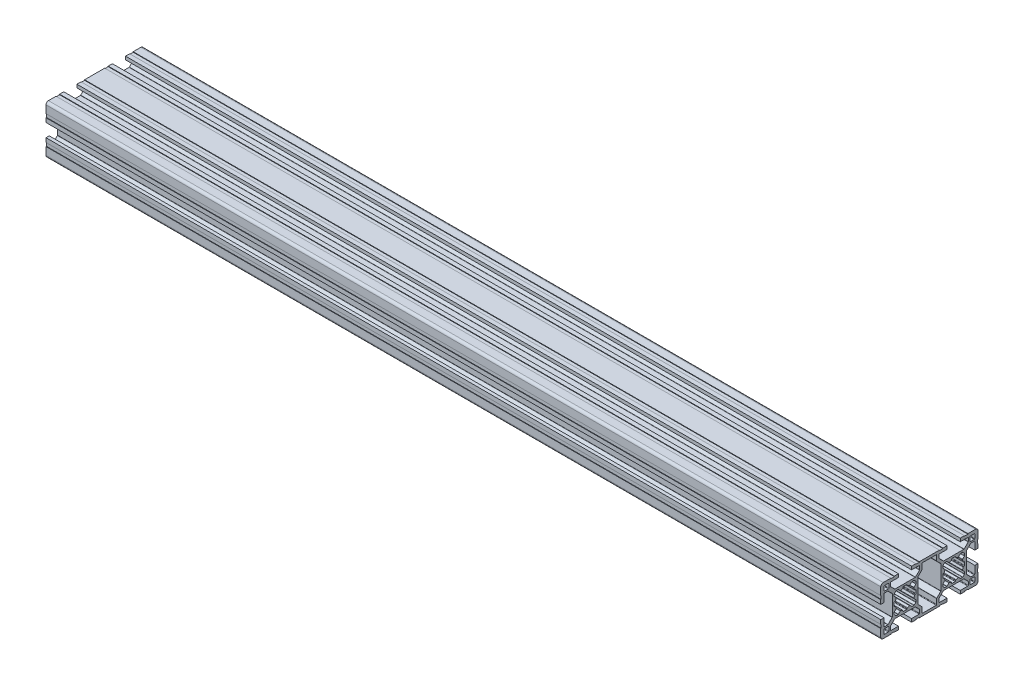
SolidWorks part; units mm, degrees
material "6063-T5 (Padrão)"
ref_plane "Plano frontal" through (0, 0, 0) normal (0, 0, 1) x (1, 0, 0)
ref_plane "Plano superior" through (0, 0, 0) normal (0, 1, 0) x (1, 0, 0)
ref_plane "Plano direito" through (0, 0, 0) normal (1, 0, 0) x (0, 0, -1)
sketch "Esboço1" plane through (0, 0, 0) normal (0, 0, 1) x (1, 0, 0)
  line L0 (-257.5, 0) -> (257.5, 0)
  point P4 (0, 0)
  dimension "D1" = 515
other "Retangular PF30-02 - PERFIL 3060 BÁSICO(1)"
ref_plane "Plano1" through (-257.5, 0, 0) normal (1, 0, 0) x (0, 1, 0)
sketch "Sketch11" plane through (-257.5, 0, 0) normal (1, 0, 0) x (0, 1, 0)
  line L0 (-9.8464, -4.5906) -> (-7.4222, -7.0149)
  line L1 (-7.21, -7.1028) -> (7.21, -7.1028)
  line L2 (7.4222, -7.0149) -> (9.8464, -4.5906)
  line L3 (10.0586, -4.5028) -> (13.2, -4.5028)
  line L4 (13.5, -4.2028) -> (13.5, 4.1972)
  line L5 (13.2, 4.4972) -> (10.0586, 4.4972)
  line L6 (9.8464, 4.5851) -> (7.4222, 7.0094)
  line L7 (7.21, 7.0972) -> (-7.21, 7.0972)
  line L8 (-7.4222, 7.0094) -> (-9.8464, 4.5851)
  line L9 (-10.0586, 4.4972) -> (-13.2, 4.4972)
  line L10 (-13.5, 4.1972) -> (-13.5, -4.2028)
  line L11 (-13.2, -4.5028) -> (-10.0586, -4.5028)
  line L12 (-6.7, 15.9528) -> (-6.7, 14.0528)
  line L13 (-6.1579, 16.2528) -> (-6.4, 16.2528)
  line L14 (-6.6121, 19.14) -> (-5.4871, 18.015)
  line L15 (-6.7, 20.4423) -> (-6.7, 19.3522)
  line L16 (-6.1319, 21.1347) -> (-6.6121, 20.6545)
  line L17 (-10.4678, 23.9149) -> (-7.9879, 21.435)
  line L18 (-12.7, 24.0028) -> (-10.6799, 24.0028)
  line L19 (-13, 19.0528) -> (-13, 23.7028)
  line L20 (-13, 19.0528) -> (-15, 19.0528)
  line L21 (6.7, 15.9528) -> (6.7, 14.0528)
  line L22 (7.9, 21.2229) -> (7.9, 8.7827)
  line L23 (15, 21.6028) -> (15, 19.0528)
  line L24 (-5.4396, 21.7028) -> (-4.3494, 21.7028)
  line L25 (-13, 25.3028) -> (-13, 27.7028)
  line L26 (-4.05, 28.0028) -> (-8.7, 28.0028)
  line L27 (-12.7, 28.0028) -> (-10.3, 28.0028)
  line L28 (-9, 27.7028) -> (-9, 25.6827)
  line L29 (-10, 27.7028) -> (-10, 25.3028)
  line L30 (-8.9121, 25.4705) -> (-6.4322, 22.9906)
  line L31 (15, 23.8028) -> (14.7, 23.8028)
  line L32 (14.7, 23.8028) -> (14.7, 21.6028)
  line L33 (15, 28.5028) -> (15, 23.8028)
  line L34 (8.8, 30.0028) -> (13.5, 30.0028)
  line L35 (8.8, 29.7028) -> (6.6, 29.7028)
  line L36 (4.05, 30.0028) -> (6.6, 30.0028)
  line L37 (4.05, 28.0028) -> (4.05, 30.0028)
  line L38 (10.3, 25.0028) -> (12.7, 25.0028)
  line L39 (15, 21.6028) -> (14.7, 21.6028)
  line L40 (6.6, 30.0028) -> (6.6, 29.7028)
  line L41 (-6.1319, 21.1347) -> (-5.6517, 21.6149)
  line L42 (-4.1373, 21.6149) -> (-3.0123, 20.4899)
  line L43 (-1.25, 21.1607) -> (-1.25, 21.4028)
  line L44 (8.8, 30.0028) -> (8.8, 29.7028)
  line L45 (1.25, 21.1607) -> (1.25, 21.4028)
  line L46 (4.1373, 21.6149) -> (3.0123, 20.4899)
  line L47 (6.1319, 21.1347) -> (5.6517, 21.6149)
  line L48 (8.9121, 25.4705) -> (6.4322, 22.9906)
  line L49 (10, 27.7028) -> (10, 25.3028)
  line L50 (9, 27.7028) -> (9, 25.6827)
  line L51 (12.7, 28.0028) -> (10.3, 28.0028)
  line L52 (4.05, 28.0028) -> (8.7, 28.0028)
  line L53 (13, 25.3028) -> (13, 27.7028)
  line L54 (5.4396, 21.7028) -> (4.3494, 21.7028)
  line L55 (13, 19.0528) -> (15, 19.0528)
  line L56 (13, 19.0528) -> (13, 23.7028)
  line L57 (12.7, 24.0028) -> (10.6799, 24.0028)
  line L58 (10.4678, 23.9149) -> (7.9879, 21.435)
  line L59 (6.1319, 21.1347) -> (6.6121, 20.6545)
  line L60 (6.7, 20.4423) -> (6.7, 19.3522)
  line L61 (6.6121, 19.14) -> (5.4871, 18.015)
  line L62 (6.1579, 16.2528) -> (6.4, 16.2528)
  line L63 (-7.9, 8.7827) -> (-7.9, 21.2229)
  line L64 (-0.95, 8.3028) -> (0.95, 8.3028)
  line L65 (-15, 8.4028) -> (-15, 10.9528)
  line L66 (-15, 6.2028) -> (-14.7, 6.2028)
  line L67 (-14.7, 6.2028) -> (-14.7, 8.4028)
  line L68 (-15, -14.9972) -> (15, -14.9972) construction
  line L69 (-6.1579, -13.7472) -> (-6.4, -13.7472)
  line L70 (-6.6121, -10.86) -> (-5.4871, -11.985)
  line L71 (-6.7, -9.5577) -> (-6.7, -10.6478)
  line L72 (-15, 8.4028) -> (-14.7, 8.4028)
  line L73 (-0.95, -21.6972) -> (0.95, -21.6972)
  line L74 (-6.1319, -8.8653) -> (-6.6121, -9.3455)
  line L75 (6.1579, 13.7528) -> (6.4, 13.7528)
  line L76 (6.6121, 10.8655) -> (5.4871, 11.9905)
  line L77 (6.7, 9.5632) -> (6.7, 10.6534)
  line L78 (6.1319, 8.8709) -> (6.6121, 9.3511)
  line L79 (10.4678, 6.0906) -> (7.9879, 8.5705)
  line L80 (12.7, 6.0028) -> (10.6799, 6.0028)
  line L81 (13, 10.9528) -> (13, 6.3028)
  line L82 (13, 10.9528) -> (15, 10.9528)
  line L83 (5.4396, 8.3028) -> (4.3494, 8.3028)
  line L84 (-10.4678, -6.0851) -> (-7.9879, -8.565)
  line L85 (-8.8, 30.0028) -> (-8.8, 29.7028)
  line L86 (-12.7, -5.9972) -> (-10.6799, -5.9972)
  line L87 (-13, -10.9472) -> (-13, -6.2972)
  line L88 (-13, -10.9472) -> (-15, -10.9472)
  line L89 (15, -8.3972) -> (15, -10.9472)
  line L90 (-5.4396, -8.2972) -> (-4.3494, -8.2972)
  line L91 (6.1319, 8.8709) -> (5.6517, 8.3906)
  line L92 (4.1373, 8.3906) -> (3.0123, 9.5156)
  line L93 (1.25, 8.8448) -> (1.25, 8.6028)
  line L94 (-15, -21.5972) -> (-15, -19.0472)
  line L95 (-6.6, 30.0028) -> (-6.6, 29.7028)
  line L96 (-1.25, 8.8448) -> (-1.25, 8.6028)
  line L97 (-4.1373, 8.3906) -> (-3.0123, 9.5156)
  line L98 (-6.1319, 8.8709) -> (-5.6517, 8.3906)
  line L99 (-15, -23.7972) -> (-14.7, -23.7972)
  line L100 (15, 8.4028) -> (14.7, 8.4028)
  line L101 (-14.7, -23.7972) -> (-14.7, -21.5972)
  line L102 (-15, -28.4972) -> (-15, -23.7972)
  line L103 (-8.8, -29.9972) -> (-13.5, -29.9972)
  line L104 (-8.8, -29.6972) -> (-6.6, -29.6972)
  line L105 (-4.05, -29.9972) -> (-6.6, -29.9972)
  line L106 (14.7, 6.2028) -> (14.7, 8.4028)
  line L107 (15, 6.2028) -> (14.7, 6.2028)
  line L108 (-4.05, -27.9972) -> (-4.05, -29.9972)
  line L109 (-10.3, -24.9972) -> (-12.7, -24.9972)
  line L110 (-6.2201, -22.8972) -> (6.2201, -22.8972)
  line L111 (-15, -21.5972) -> (-14.7, -21.5972)
  line L112 (15, -6.1972) -> (14.7, -6.1972)
  line L113 (-15, 21.6028) -> (-14.7, 21.6028)
  line L114 (-6.2201, 22.9028) -> (6.2201, 22.9028)
  line L115 (-10.3, 25.0028) -> (-12.7, 25.0028)
  line L116 (-4.05, 28.0028) -> (-4.05, 30.0028)
  line L117 (-4.05, 30.0028) -> (-6.6, 30.0028)
  line L118 (-8.8, 29.7028) -> (-6.6, 29.7028)
  line L119 (0, 29.9972) -> (0, -29.9972) construction
  line L120 (-15, 15.0028) -> (15, 15.0028) construction
  line L121 (-8.8, 30.0028) -> (-13.5, 30.0028)
  line L122 (-15, 28.5028) -> (-15, 23.8028)
  line L123 (-14.7, 23.8028) -> (-14.7, 21.6028)
  line L124 (-15, 23.8028) -> (-14.7, 23.8028)
  line L125 (-15, 21.6028) -> (-15, 19.0528)
  line L126 (14.7, -6.1972) -> (14.7, -8.3972)
  line L127 (-5.4396, 8.3028) -> (-4.3494, 8.3028)
  line L128 (15, 8.4028) -> (15, 10.9528)
  line L129 (15, 6.2028) -> (15, -6.1972)
  line L130 (-13, 10.9528) -> (-15, 10.9528)
  line L131 (-13, 10.9528) -> (-13, 6.3028)
  line L132 (-12.7, 6.0028) -> (-10.6799, 6.0028)
  line L133 (-10.4678, 6.0906) -> (-7.9879, 8.5705)
  line L134 (-6.1319, 8.8709) -> (-6.6121, 9.3511)
  line L135 (-0.95, 21.7028) -> (0.95, 21.7028)
  line L136 (-6.7, 9.5632) -> (-6.7, 10.6534)
  line L137 (-6.6121, 10.8655) -> (-5.4871, 11.9905)
  line L138 (-6.1579, 13.7528) -> (-6.4, 13.7528)
  line L139 (15, 0.0028) -> (-15, 0.0028) construction
  line L140 (15, -8.3972) -> (14.7, -8.3972)
  line L141 (-6.1319, -8.8653) -> (-5.6517, -8.3851)
  line L142 (-4.1373, -8.3851) -> (-3.0123, -9.5101)
  line L143 (-1.25, -8.8393) -> (-1.25, -8.5972)
  line L144 (-6.6, -29.9972) -> (-6.6, -29.6972)
  line L145 (1.25, -8.8393) -> (1.25, -8.5972)
  line L146 (4.1373, -8.3851) -> (3.0123, -9.5101)
  line L147 (6.1319, -8.8653) -> (5.6517, -8.3851)
  line L148 (-8.8, -29.9972) -> (-8.8, -29.6972)
  line L149 (5.4396, -8.2972) -> (4.3494, -8.2972)
  line L150 (13, -10.9472) -> (15, -10.9472)
  line L151 (13, -10.9472) -> (13, -6.2972)
  line L152 (12.7, -5.9972) -> (10.6799, -5.9972)
  line L153 (10.4678, -6.0851) -> (7.9879, -8.565)
  line L154 (6.1319, -8.8653) -> (6.6121, -9.3455)
  line L155 (6.7, -9.5577) -> (6.7, -10.6478)
  line L156 (6.6121, -10.86) -> (5.4871, -11.985)
  line L157 (6.1579, -13.7472) -> (6.4, -13.7472)
  line L158 (-15, -8.3972) -> (-14.7, -8.3972)
  line L159 (-15, 6.2028) -> (-15, -6.1972)
  line L160 (-14.7, -6.1972) -> (-14.7, -8.3972)
  line L161 (-15, -6.1972) -> (-14.7, -6.1972)
  line L162 (-15, -8.3972) -> (-15, -10.9472)
  line L163 (-0.95, -8.2972) -> (0.95, -8.2972)
  line L164 (-7.9, -8.7771) -> (-7.9, -21.2173)
  line L165 (6.1579, -16.2472) -> (6.4, -16.2472)
  line L166 (6.6121, -19.1345) -> (5.4871, -18.0095)
  line L167 (6.7, -20.4368) -> (6.7, -19.3466)
  line L168 (6.1319, -21.1291) -> (6.6121, -20.6489)
  line L169 (10.4678, -23.9094) -> (7.9879, -21.4295)
  line L170 (12.7, -23.9972) -> (10.6799, -23.9972)
  line L171 (13, -19.0472) -> (13, -23.6972)
  line L172 (13, -19.0472) -> (15, -19.0472)
  line L173 (5.4396, -21.6972) -> (4.3494, -21.6972)
  line L174 (13, -25.2972) -> (13, -27.6972)
  line L175 (4.05, -27.9972) -> (8.7, -27.9972)
  line L176 (12.7, -27.9972) -> (10.3, -27.9972)
  line L177 (9, -27.6972) -> (9, -25.6771)
  line L178 (10, -27.6972) -> (10, -25.2972)
  line L179 (8.9121, -25.465) -> (6.4322, -22.9851)
  line L180 (6.1319, -21.1291) -> (5.6517, -21.6093)
  line L181 (4.1373, -21.6093) -> (3.0123, -20.4844)
  line L182 (1.25, -21.1551) -> (1.25, -21.3972)
  line L183 (8.8, -29.9972) -> (8.8, -29.6972)
  line L184 (-1.25, -21.1551) -> (-1.25, -21.3972)
  line L185 (-4.1373, -21.6093) -> (-3.0123, -20.4844)
  line L186 (-6.1319, -21.1291) -> (-5.6517, -21.6093)
  line L187 (6.6, -29.9972) -> (6.6, -29.6972)
  line L188 (15, -21.5972) -> (14.7, -21.5972)
  line L189 (10.3, -24.9972) -> (12.7, -24.9972)
  line L190 (4.05, -27.9972) -> (4.05, -29.9972)
  line L191 (4.05, -29.9972) -> (6.6, -29.9972)
  line L192 (8.8, -29.6972) -> (6.6, -29.6972)
  line L193 (8.8, -29.9972) -> (13.5, -29.9972)
  line L194 (15, -28.4972) -> (15, -23.7972)
  line L195 (14.7, -23.7972) -> (14.7, -21.5972)
  line L196 (15, -23.7972) -> (14.7, -23.7972)
  line L197 (-8.9121, -25.465) -> (-6.4322, -22.9851)
  line L198 (-10, -27.6972) -> (-10, -25.2972)
  line L199 (-9, -27.6972) -> (-9, -25.6771)
  line L200 (-12.7, -27.9972) -> (-10.3, -27.9972)
  line L201 (-4.05, -27.9972) -> (-8.7, -27.9972)
  line L202 (-13, -25.2972) -> (-13, -27.6972)
  line L203 (-5.4396, -21.6972) -> (-4.3494, -21.6972)
  line L204 (15, -21.5972) -> (15, -19.0472)
  line L205 (7.9, -21.2173) -> (7.9, -8.7771)
  line L206 (6.7, -15.9472) -> (6.7, -14.0472)
  line L207 (-13, -19.0472) -> (-15, -19.0472)
  line L208 (-13, -19.0472) -> (-13, -23.6972)
  line L209 (-12.7, -23.9972) -> (-10.6799, -23.9972)
  line L210 (-10.4678, -23.9094) -> (-7.9879, -21.4295)
  line L211 (-6.1319, -21.1291) -> (-6.6121, -20.6489)
  line L212 (-6.7, -20.4368) -> (-6.7, -19.3466)
  line L213 (-6.6121, -19.1345) -> (-5.4871, -18.0095)
  line L214 (-6.1579, -16.2472) -> (-6.4, -16.2472)
  line L215 (-6.7, -15.9472) -> (-6.7, -14.0472)
  arc A0 (-9.8464, -4.5906) -> (-10.0586, -4.5028) centre (-10.0586, -4.8028) ccw
  arc A1 (-7.4222, -7.0149) -> (-7.21, -7.1028) centre (-7.21, -6.8028) ccw
  arc A2 (7.21, -7.1028) -> (7.4222, -7.0149) centre (7.21, -6.8028) ccw
  arc A3 (10.0586, -4.5028) -> (9.8464, -4.5906) centre (10.0586, -4.8028) ccw
  arc A4 (13.2, -4.5028) -> (13.5, -4.2028) centre (13.2, -4.2028) ccw
  arc A5 (13.5, 4.1972) -> (13.2, 4.4972) centre (13.2, 4.1972) ccw
  arc A6 (9.8464, 4.5851) -> (10.0586, 4.4972) centre (10.0586, 4.7972) ccw
  arc A7 (7.4222, 7.0094) -> (7.21, 7.0972) centre (7.21, 6.7972) ccw
  arc A8 (-7.21, 7.0972) -> (-7.4222, 7.0094) centre (-7.21, 6.7972) ccw
  arc A9 (-10.0586, 4.4972) -> (-9.8464, 4.5851) centre (-10.0586, 4.7972) ccw
  arc A10 (-13.2, 4.4972) -> (-13.5, 4.1972) centre (-13.2, 4.1972) ccw
  arc A11 (-13.5, -4.2028) -> (-13.2, -4.5028) centre (-13.2, -4.2028) ccw
  arc A12 (-6.4, 16.2528) -> (-6.7, 15.9528) centre (-6.4, 15.9528) ccw
  arc A13 (-5.867, 16.4795) -> (-6.1579, 16.2528) centre (-6.1579, 16.5528) cw
  arc A14 (-5.867, 16.4795) -> (-5.43, 17.6706) centre (0, 15.0028) cw
  arc A15 (-5.4871, 18.015) -> (-5.43, 17.6706) centre (-5.6993, 17.8029) cw
  arc A16 (-6.6121, 19.14) -> (-6.7, 19.3522) centre (-6.4, 19.3522) cw
  arc A17 (-6.6121, 20.6545) -> (-6.7, 20.4423) centre (-6.4, 20.4423) ccw
  arc A18 (-7.9879, 21.435) -> (-7.9, 21.2229) centre (-8.2, 21.2229) cw
  arc A19 (-10.6799, 24.0028) -> (-10.4678, 23.9149) centre (-10.6799, 23.7028) cw
  arc A20 (-13, 23.7028) -> (-12.7, 24.0028) centre (-12.7, 23.7028) cw
  arc A21 (13.5, 30.0028) -> (15, 28.5028) centre (13.5, 28.5028) cw
  arc A22 (1.25, 21.4028) -> (0.95, 21.7028) centre (0.95, 21.4028) ccw
  arc A23 (4.1373, 21.6149) -> (4.3494, 21.7028) centre (4.3494, 21.4028) cw
  arc A24 (1.4768, 20.8698) -> (1.25, 21.1607) centre (1.55, 21.1607) cw
  arc A25 (1.4768, 20.8698) -> (2.6678, 20.4328) centre (0, 15.0028) cw
  arc A26 (-10.3, 25.0028) -> (-10, 25.3028) centre (-10.3, 25.3028) ccw
  arc A27 (-6.4322, 22.9906) -> (-6.2201, 22.9028) centre (-6.2201, 23.2028) ccw
  arc A28 (-13, 25.3028) -> (-12.7, 25.0028) centre (-12.7, 25.3028) ccw
  arc A29 (-9, 25.6827) -> (-8.9121, 25.4705) centre (-8.7, 25.6827) ccw
  arc A30 (-10, 27.7028) -> (-10.3, 28.0028) centre (-10.3, 27.7028) ccw
  arc A31 (-8.7, 28.0028) -> (-9, 27.7028) centre (-8.7, 27.7028) ccw
  arc A32 (-12.7, 28.0028) -> (-13, 27.7028) centre (-12.7, 27.7028) ccw
  arc A33 (3.0123, 20.4899) -> (2.6678, 20.4328) centre (2.8001, 20.702) cw
  arc A34 (5.6517, 21.6149) -> (5.4396, 21.7028) centre (5.4396, 21.4028) ccw
  arc A35 (12.7, 28.0028) -> (13, 27.7028) centre (12.7, 27.7028) cw
  arc A36 (8.7, 28.0028) -> (9, 27.7028) centre (8.7, 27.7028) cw
  arc A37 (10, 27.7028) -> (10.3, 28.0028) centre (10.3, 27.7028) cw
  arc A38 (9, 25.6827) -> (8.9121, 25.4705) centre (8.7, 25.6827) cw
  arc A39 (13, 25.3028) -> (12.7, 25.0028) centre (12.7, 25.3028) cw
  arc A40 (6.4322, 22.9906) -> (6.2201, 22.9028) centre (6.2201, 23.2028) cw
  arc A41 (10.3, 25.0028) -> (10, 25.3028) centre (10.3, 25.3028) cw
  arc A42 (13, 23.7028) -> (12.7, 24.0028) centre (12.7, 23.7028) ccw
  arc A43 (10.6799, 24.0028) -> (10.4678, 23.9149) centre (10.6799, 23.7028) ccw
  arc A44 (7.9879, 21.435) -> (7.9, 21.2229) centre (8.2, 21.2229) ccw
  arc A45 (6.6121, 20.6545) -> (6.7, 20.4423) centre (6.4, 20.4423) cw
  arc A46 (6.6121, 19.14) -> (6.7, 19.3522) centre (6.4, 19.3522) ccw
  arc A47 (5.4871, 18.015) -> (5.43, 17.6706) centre (5.6993, 17.8029) ccw
  arc A48 (5.867, 16.4795) -> (5.43, 17.6706) centre (0, 15.0028) ccw
  arc A49 (5.867, 16.4795) -> (6.1579, 16.2528) centre (6.1579, 16.5528) ccw
  arc A50 (6.4, 16.2528) -> (6.7, 15.9528) centre (6.4, 15.9528) cw
  arc A51 (6.4, 13.7528) -> (6.7, 14.0528) centre (6.4, 14.0528) ccw
  arc A52 (-5.6517, 21.6149) -> (-5.4396, 21.7028) centre (-5.4396, 21.4028) cw
  arc A53 (-3.0123, 20.4899) -> (-2.6678, 20.4328) centre (-2.8001, 20.702) ccw
  arc A54 (-1.4768, 20.8698) -> (-2.6678, 20.4328) centre (0, 15.0028) ccw
  arc A55 (-1.4768, 20.8698) -> (-1.25, 21.1607) centre (-1.55, 21.1607) ccw
  arc A56 (-4.1373, 21.6149) -> (-4.3494, 21.7028) centre (-4.3494, 21.4028) ccw
  arc A57 (-6.4, 13.7528) -> (-6.7, 14.0528) centre (-6.4, 14.0528) cw
  arc A58 (-13.5, -29.9972) -> (-15, -28.4972) centre (-13.5, -28.4972) cw
  arc A59 (-1.25, 8.6028) -> (-0.95, 8.3028) centre (-0.95, 8.6028) ccw
  arc A60 (-4.1373, 8.3906) -> (-4.3494, 8.3028) centre (-4.3494, 8.6028) cw
  arc A61 (-1.4768, 9.1358) -> (-1.25, 8.8448) centre (-1.55, 8.8448) cw
  arc A62 (-1.4768, 9.1358) -> (-2.6678, 9.5728) centre (0, 15.0028) cw
  arc A63 (-3.0123, 9.5156) -> (-2.6678, 9.5728) centre (-2.8001, 9.3035) cw
  arc A64 (-5.6517, 8.3906) -> (-5.4396, 8.3028) centre (-5.4396, 8.6028) ccw
  arc A65 (5.867, 13.526) -> (6.1579, 13.7528) centre (6.1579, 13.4528) cw
  arc A66 (5.867, 13.526) -> (5.43, 12.3349) centre (0, 15.0028) cw
  arc A67 (5.4871, 11.9905) -> (5.43, 12.3349) centre (5.6993, 12.2026) cw
  arc A68 (6.6121, 10.8655) -> (6.7, 10.6534) centre (6.4, 10.6534) cw
  arc A69 (6.6121, 9.3511) -> (6.7, 9.5632) centre (6.4, 9.5632) ccw
  arc A70 (7.9879, 8.5705) -> (7.9, 8.7827) centre (8.2, 8.7827) cw
  arc A71 (10.6799, 6.0028) -> (10.4678, 6.0906) centre (10.6799, 6.3028) cw
  arc A72 (13, 6.3028) -> (12.7, 6.0028) centre (12.7, 6.3028) cw
  arc A73 (-5.867, -13.5205) -> (-6.1579, -13.7472) centre (-6.1579, -13.4472) cw
  arc A74 (-5.867, -13.5205) -> (-5.43, -12.3294) centre (0, -14.9972) cw
  arc A75 (-1.25, -21.3972) -> (-0.95, -21.6972) centre (-0.95, -21.3972) ccw
  arc A76 (-5.4871, -11.985) -> (-5.43, -12.3294) centre (-5.6993, -12.1971) cw
  arc A77 (-6.6121, -10.86) -> (-6.7, -10.6478) centre (-6.4, -10.6478) cw
  arc A78 (-6.6121, -9.3455) -> (-6.7, -9.5577) centre (-6.4, -9.5577) ccw
  arc A79 (-7.9879, -8.565) -> (-7.9, -8.7771) centre (-8.2, -8.7771) cw
  arc A80 (5.6517, 8.3906) -> (5.4396, 8.3028) centre (5.4396, 8.6028) cw
  arc A81 (3.0123, 9.5156) -> (2.6678, 9.5728) centre (2.8001, 9.3035) ccw
  arc A82 (-10.6799, -5.9972) -> (-10.4678, -6.0851) centre (-10.6799, -6.2972) cw
  arc A83 (-13, -6.2972) -> (-12.7, -5.9972) centre (-12.7, -6.2972) cw
  arc A84 (1.25, -8.5972) -> (0.95, -8.2972) centre (0.95, -8.5972) ccw
  arc A85 (4.1373, -8.3851) -> (4.3494, -8.2972) centre (4.3494, -8.5972) cw
  arc A86 (1.4768, -9.1302) -> (1.25, -8.8393) centre (1.55, -8.8393) cw
  arc A87 (1.4768, -9.1302) -> (2.6678, -9.5672) centre (0, -14.9972) cw
  arc A88 (3.0123, -9.5101) -> (2.6678, -9.5672) centre (2.8001, -9.2979) cw
  arc A89 (1.4768, 9.1358) -> (2.6678, 9.5728) centre (0, 15.0028) ccw
  arc A90 (1.4768, 9.1358) -> (1.25, 8.8448) centre (1.55, 8.8448) ccw
  arc A91 (4.1373, 8.3906) -> (4.3494, 8.3028) centre (4.3494, 8.6028) ccw
  arc A92 (1.25, 8.6028) -> (0.95, 8.3028) centre (0.95, 8.6028) cw
  arc A93 (5.6517, -8.3851) -> (5.4396, -8.2972) centre (5.4396, -8.5972) ccw
  arc A94 (-13, 6.3028) -> (-12.7, 6.0028) centre (-12.7, 6.3028) ccw
  arc A95 (-10.6799, 6.0028) -> (-10.4678, 6.0906) centre (-10.6799, 6.3028) ccw
  arc A96 (-7.9879, 8.5705) -> (-7.9, 8.7827) centre (-8.2, 8.7827) ccw
  arc A97 (-6.6121, 9.3511) -> (-6.7, 9.5632) centre (-6.4, 9.5632) cw
  arc A98 (-6.6121, 10.8655) -> (-6.7, 10.6534) centre (-6.4, 10.6534) ccw
  arc A99 (-5.4871, 11.9905) -> (-5.43, 12.3349) centre (-5.6993, 12.2026) ccw
  arc A100 (-1.25, 21.4028) -> (-0.95, 21.7028) centre (-0.95, 21.4028) cw
  arc A101 (-5.867, 13.526) -> (-5.43, 12.3349) centre (0, 15.0028) ccw
  arc A102 (-5.867, 13.526) -> (-6.1579, 13.7528) centre (-6.1579, 13.4528) ccw
  arc A103 (-13.5, 30.0028) -> (-15, 28.5028) centre (-13.5, 28.5028) ccw
  arc A104 (13, -6.2972) -> (12.7, -5.9972) centre (12.7, -6.2972) ccw
  arc A105 (10.6799, -5.9972) -> (10.4678, -6.0851) centre (10.6799, -6.2972) ccw
  arc A106 (7.9879, -8.565) -> (7.9, -8.7771) centre (8.2, -8.7771) ccw
  arc A107 (6.6121, -9.3455) -> (6.7, -9.5577) centre (6.4, -9.5577) cw
  arc A108 (6.6121, -10.86) -> (6.7, -10.6478) centre (6.4, -10.6478) ccw
  arc A109 (5.4871, -11.985) -> (5.43, -12.3294) centre (5.6993, -12.1971) ccw
  arc A110 (5.867, -13.5205) -> (5.43, -12.3294) centre (0, -14.9972) ccw
  arc A111 (5.867, -13.5205) -> (6.1579, -13.7472) centre (6.1579, -13.4472) ccw
  arc A112 (-5.6517, -8.3851) -> (-5.4396, -8.2972) centre (-5.4396, -8.5972) cw
  arc A113 (-3.0123, -9.5101) -> (-2.6678, -9.5672) centre (-2.8001, -9.2979) ccw
  arc A114 (-1.4768, -9.1302) -> (-2.6678, -9.5672) centre (0, -14.9972) ccw
  arc A115 (-1.4768, -9.1302) -> (-1.25, -8.8393) centre (-1.55, -8.8393) ccw
  arc A116 (-4.1373, -8.3851) -> (-4.3494, -8.2972) centre (-4.3494, -8.5972) ccw
  arc A117 (-1.25, -8.5972) -> (-0.95, -8.2972) centre (-0.95, -8.5972) cw
  arc A118 (-6.4, -13.7472) -> (-6.7, -14.0472) centre (-6.4, -14.0472) ccw
  arc A119 (-4.1373, -21.6093) -> (-4.3494, -21.6972) centre (-4.3494, -21.3972) cw
  arc A120 (-1.4768, -20.8642) -> (-1.25, -21.1551) centre (-1.55, -21.1551) cw
  arc A121 (-1.4768, -20.8642) -> (-2.6678, -20.4272) centre (0, -14.9972) cw
  arc A122 (-3.0123, -20.4844) -> (-2.6678, -20.4272) centre (-2.8001, -20.6965) cw
  arc A123 (-5.6517, -21.6093) -> (-5.4396, -21.6972) centre (-5.4396, -21.3972) ccw
  arc A124 (6.4, -13.7472) -> (6.7, -14.0472) centre (6.4, -14.0472) cw
  arc A125 (6.4, -16.2472) -> (6.7, -15.9472) centre (6.4, -15.9472) ccw
  arc A126 (5.867, -16.474) -> (6.1579, -16.2472) centre (6.1579, -16.5472) cw
  arc A127 (5.867, -16.474) -> (5.43, -17.6651) centre (0, -14.9972) cw
  arc A128 (5.4871, -18.0095) -> (5.43, -17.6651) centre (5.6993, -17.7974) cw
  arc A129 (6.6121, -19.1345) -> (6.7, -19.3466) centre (6.4, -19.3466) cw
  arc A130 (6.6121, -20.6489) -> (6.7, -20.4368) centre (6.4, -20.4368) ccw
  arc A131 (7.9879, -21.4295) -> (7.9, -21.2173) centre (8.2, -21.2173) cw
  arc A132 (10.6799, -23.9972) -> (10.4678, -23.9094) centre (10.6799, -23.6972) cw
  arc A133 (13, -23.6972) -> (12.7, -23.9972) centre (12.7, -23.6972) cw
  arc A134 (10.3, -24.9972) -> (10, -25.2972) centre (10.3, -25.2972) ccw
  arc A135 (6.4322, -22.9851) -> (6.2201, -22.8972) centre (6.2201, -23.1972) ccw
  arc A136 (13, -25.2972) -> (12.7, -24.9972) centre (12.7, -25.2972) ccw
  arc A137 (9, -25.6771) -> (8.9121, -25.465) centre (8.7, -25.6771) ccw
  arc A138 (10, -27.6972) -> (10.3, -27.9972) centre (10.3, -27.6972) ccw
  arc A139 (8.7, -27.9972) -> (9, -27.6972) centre (8.7, -27.6972) ccw
  arc A140 (12.7, -27.9972) -> (13, -27.6972) centre (12.7, -27.6972) ccw
  arc A141 (5.6517, -21.6093) -> (5.4396, -21.6972) centre (5.4396, -21.3972) cw
  arc A142 (3.0123, -20.4844) -> (2.6678, -20.4272) centre (2.8001, -20.6965) ccw
  arc A143 (-12.7, -27.9972) -> (-13, -27.6972) centre (-12.7, -27.6972) cw
  arc A144 (-8.7, -27.9972) -> (-9, -27.6972) centre (-8.7, -27.6972) cw
  arc A145 (-10, -27.6972) -> (-10.3, -27.9972) centre (-10.3, -27.6972) cw
  arc A146 (-9, -25.6771) -> (-8.9121, -25.465) centre (-8.7, -25.6771) cw
  arc A147 (-13, -25.2972) -> (-12.7, -24.9972) centre (-12.7, -25.2972) cw
  arc A148 (-6.4322, -22.9851) -> (-6.2201, -22.8972) centre (-6.2201, -23.1972) cw
  arc A149 (-10.3, -24.9972) -> (-10, -25.2972) centre (-10.3, -25.2972) cw
  arc A150 (1.4768, -20.8642) -> (2.6678, -20.4272) centre (0, -14.9972) ccw
  arc A151 (1.4768, -20.8642) -> (1.25, -21.1551) centre (1.55, -21.1551) ccw
  arc A152 (4.1373, -21.6093) -> (4.3494, -21.6972) centre (4.3494, -21.3972) ccw
  arc A153 (1.25, -21.3972) -> (0.95, -21.6972) centre (0.95, -21.3972) cw
  arc A154 (13.5, -29.9972) -> (15, -28.4972) centre (13.5, -28.4972) ccw
  arc A155 (-13, -23.6972) -> (-12.7, -23.9972) centre (-12.7, -23.6972) ccw
  arc A156 (-10.6799, -23.9972) -> (-10.4678, -23.9094) centre (-10.6799, -23.6972) ccw
  arc A157 (-7.9879, -21.4295) -> (-7.9, -21.2173) centre (-8.2, -21.2173) ccw
  arc A158 (-6.6121, -20.6489) -> (-6.7, -20.4368) centre (-6.4, -20.4368) cw
  arc A159 (-6.6121, -19.1345) -> (-6.7, -19.3466) centre (-6.4, -19.3466) ccw
  arc A160 (-5.4871, -18.0095) -> (-5.43, -17.6651) centre (-5.6993, -17.7974) ccw
  arc A161 (-5.867, -16.474) -> (-5.43, -17.6651) centre (0, -14.9972) ccw
  arc A162 (-5.867, -16.474) -> (-6.1579, -16.2472) centre (-6.1579, -16.5472) ccw
  arc A163 (-6.4, -16.2472) -> (-6.7, -15.9472) centre (-6.4, -15.9472) cw
  point P36 (-15, -14.9972)
  point P37 (0, 15.0028)
  point P66 (-11.6899, 24.0028)
  point P156 (0, 30.0028)
  point P176 (15, 30.0028)
  point P177 (11.6899, 24.0028)
  point P179 (-6.7, 15.0028)
  point P180 (6.7, 15.0028)
  point P187 (0, -0.0028)
  point P291 (15, -14.9972)
  point P315 (0, 29.9972)
  point P317 (15, 15.0028)
  point P321 (-15, 15.0028)
  point P322 (-15, 30.0028)
  point P324 (0, 15.0028)
  point P357 (-15, 0.0028)
  point P358 (0, 0.0083)
  point P359 (11.6899, 6.0028)
  point P360 (15, 0.0028)
  point P361 (0, 0.0028)
  point P362 (-11.6899, 6.0028)
  point P534 (0, -14.9972)
  point P539 (-15, -29.9972)
  point P557 (-11.6899, -5.9972)
  point P558 (11.6899, -5.9972)
  point P559 (0, -29.9917)
  point P560 (6.7, -14.9972)
  point P561 (-6.7, -14.9972)
  point P562 (11.6899, -23.9972)
  point P563 (15, -29.9972)
  point P564 (0, -29.9972)
  point P565 (-11.6899, -23.9972)
  point P566 (0, 0)
